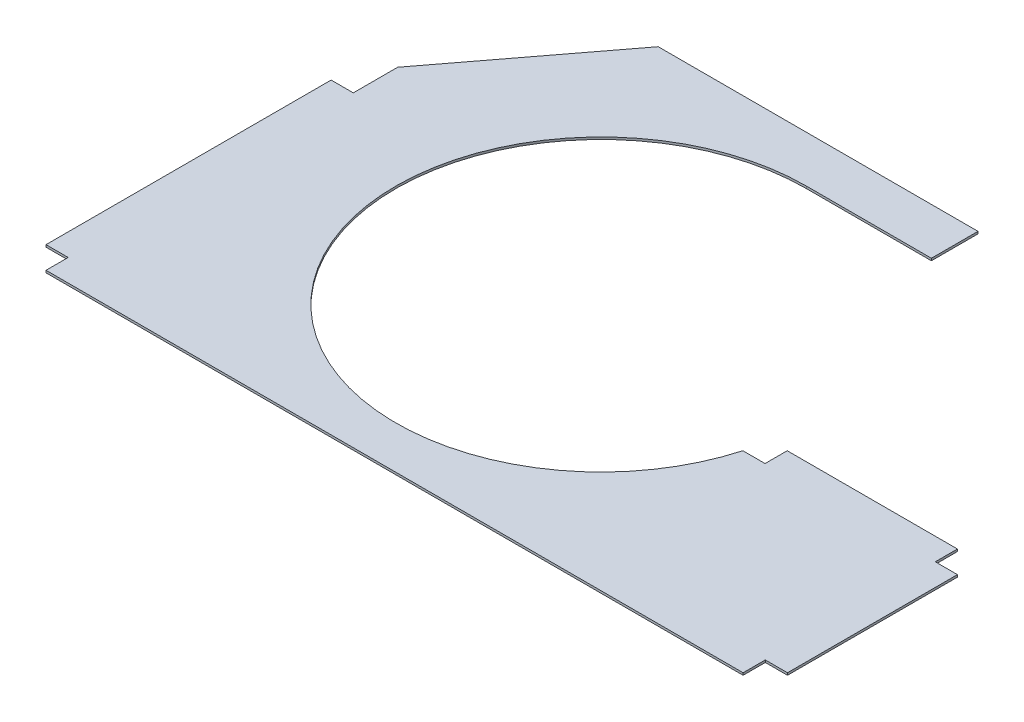
SolidWorks part; units mm, degrees
ref_plane "Front Plane" through (0, 0, 0) normal (0, 0, 1) x (1, 0, 0)
ref_plane "Top Plane" through (0, 0, 0) normal (0, 1, 0) x (1, 0, 0)
ref_plane "Right Plane" through (0, 0, 0) normal (1, 0, 0) x (0, 0, -1)
sketch "Sketch1" plane through (0, 0, 0) normal (0, 1, 0) x (1, 0, 0)
  line L0 (0, 0) -> (20, 0)
  line L1 (20, 0) -> (20, -20)
  line L2 (20, -20) -> (648.38, -20)
  line L3 (648.38, -20) -> (648.38, 0)
  line L4 (648.38, 0) -> (668.38, 0)
  line L5 (668.38, 0) -> (668.38, 153.21)
  line L7 (0, 0) -> (0, 257)
  line L9 (121.3895, 430.4594) -> (409.6583, 430.4594)
  line L10 (296.9, 388.4594) -> (409.6583, 388.4594)
  line L11 (409.6583, 430.4594) -> (409.6583, 388.4594)
  line L12 (0, 257) -> (20, 257)
  line L13 (20, 257) -> (20, 297)
  line L14 (20, 297) -> (121.3895, 430.4594)
  line L15 (668.38, 153.21) -> (648.38, 153.21)
  line L16 (648.38, 153.21) -> (648.38, 173.21)
  line L18 (648.38, 173.21) -> (494.9449, 173.21)
  line L19 (494.9449, 173.21) -> (494.9449, 153.21)
  line L20 (494.9449, 153.21) -> (474.9449, 153.21)
  arc A0 (474.9449, 153.21) -> (296.9, 388.4594) centre (296.9, 203.4594) cw
  dimension "D13" = 185
  dimension "D1" = 628.38
  dimension "D2" = 20
  dimension "D3" = 20
  dimension "D4" = 20
  dimension "D5" = 257
  dimension "D6" = 20
  dimension "D7" = 40
  dimension "D8" = 450.4594
  dimension "D9" = 153.21
  dimension "D10" = 20
  dimension "D11" = 20
  dimension "D12" = 42
  dimension "D14" = 296.9
  dimension "D15" = 20
  dimension "D16" = 20
extrude "Boss-Extrude1" add sketch "Sketch1" along normal blind 2
